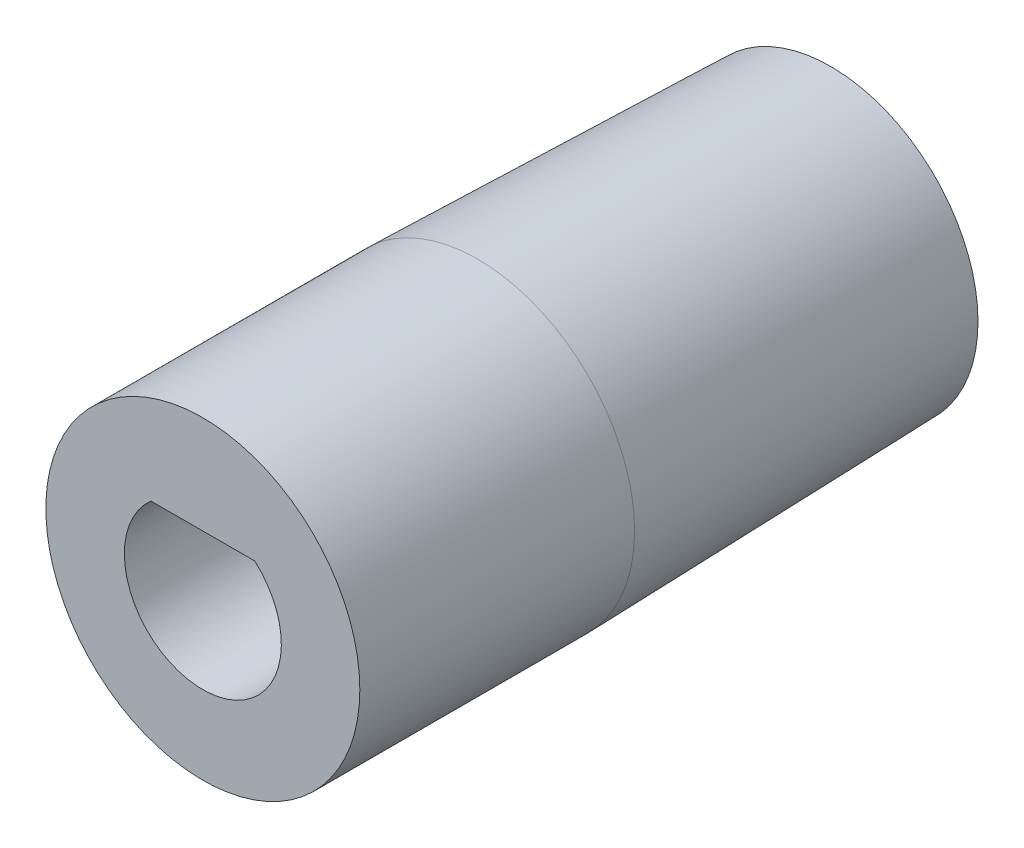
SolidWorks part; units mm, degrees
material "Сплав 2024"
ref_plane "Спереди" through (0, 0, 0) normal (0, 0, 1) x (1, 0, 0)
ref_plane "Сверху" through (0, 0, 0) normal (0, 1, 0) x (1, 0, 0)
ref_plane "Справа" through (0, 0, 0) normal (1, 0, 0) x (0, 0, -1)
sketch "Эскиз1" plane through (0, 0, 0) normal (0, 1, 0) x (1, 0, 0)
  line L0 (0, 9) -> (3.75, 9)
  line L1 (3.75, 9) -> (4, 0)
  line L2 (4, 0) -> (0, 0)
  line L3 (0, 0) -> (0, 9)
  dimension "D1" = 3.75
  dimension "D2" = 4
  dimension "D3" = 9
revolve "Повернуть1" add sketch "Эскиз1" angle 360 about L3
sketch "Эскиз6" plane through (0, 0, 0) normal (0, 0, 1) x (1, 0, 0)
  circle A0 centre (0, 0) radius 4
  circle A1 centre (0, 0) radius 4 construction
extrude "Бобышка-Вытянуть2" add sketch "Эскиз6" along normal blind 7
hole_wizard "Отверстие обработанное метчиком M4x0.72" positions "Эскиз8" profile "Эскиз7" tap size "M4x0.7" standard "Ansi Metric"
sketch "Эскиз8" plane through (0, 0, -9) normal (0, 0, -1) x (-1, 0, 0)
  point P0 (0, 0)
sketch "Эскиз7" plane through (0, 0, -9) normal (1, 0, 0) x (0, 1, 0)
  line L0 (0, 0) -> (0, 9.9914)
  line L1 (0, 9.9914) -> (1.65, 9)
  line L2 (1.65, 9) -> (1.65, 0)
  line L5 (1.65, 0) -> (0, 0)
  line L10 (0, 9.9914) -> (-1.65, 9) construction
  line L11 (0, -6.35) -> (0, 107.95) construction
  dimension "Диаметр сверла" = 3.3
  dimension "Глубина сверла" = 9
  dimension "Угол заточки сверла" = 118
cosmetic thread "Отверстие резьбы2" parameters "D1"=4.3, "D2"=4
sketch "Эскиз9" plane through (0, 0, 7) normal (0, 0, 1) x (1, 0, 0)
  line L0 (-3.9582, 1.5) -> (3.9134, 1.5) construction
  line L1 (-1.3229, 1.5) -> (1.3229, 1.5)
  arc A0 (-1.3229, 1.5) -> (1.3229, 1.5) centre (0, 0) ccw
  dimension "D1" = 4
  dimension "D2" = 1.5
extrude "Вырез-Вытянуть1" cut sketch "Эскиз9" against normal blind 7
